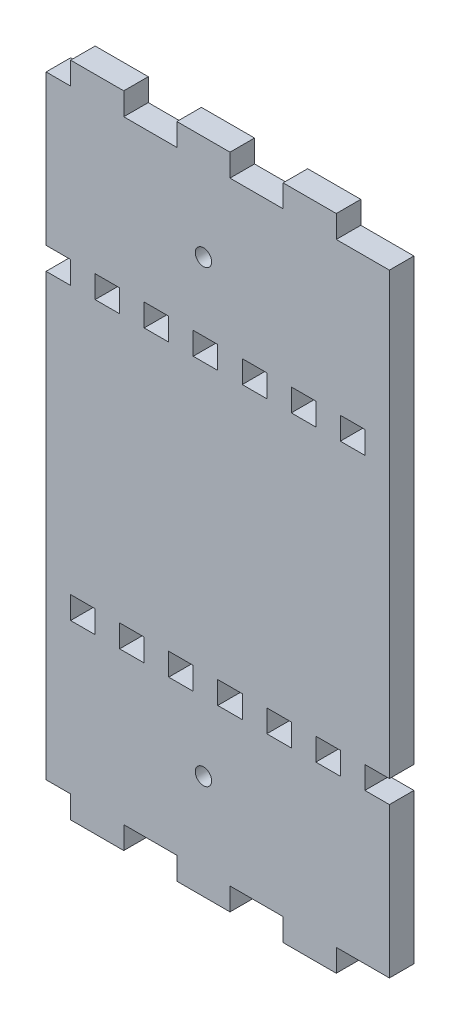
SolidWorks part; units mm, degrees
ref_plane "Front Plane" through (0, 0, 0) normal (0, 0, 1) x (1, 0, 0)
ref_plane "Top Plane" through (0, 0, 0) normal (0, 1, 0) x (1, 0, 0)
ref_plane "Right Plane" through (0, 0, 0) normal (1, 0, 0) x (0, 0, -1)
sketch "Model" plane through (0, 0, 0) normal (0, 0, 1) x (1, 0, 0)
  line L0 (-665.3097, 302.8745) -> (-665.3097, 339.6245)
  line L1 (-665.3097, 345.1245) -> (-665.3097, 452.8745)
  line L2 (-665.3097, 452.8745) -> (-678.3097, 452.8745)
  line L3 (-691.3097, 452.8745) -> (-704.3083, 452.8745)
  line L4 (-717.3083, 452.8745) -> (-730.3069, 452.8745)
  line L5 (-749.3097, 452.8745) -> (-749.3097, 416.1245)
  line L6 (-749.3097, 410.6245) -> (-749.3097, 302.8745)
  line L7 (-701.3097, 410.6245) -> (-695.3097, 410.6245)
  line L8 (-689.3097, 410.6245) -> (-683.3097, 410.6245)
  line L9 (-677.3097, 410.6245) -> (-671.3097, 410.6245)
  line L10 (-707.3097, 410.6245) -> (-713.3097, 410.6245)
  line L11 (-719.3097, 410.6245) -> (-725.3097, 410.6245)
  line L12 (-731.3097, 410.6245) -> (-737.3097, 410.6245)
  line L13 (-743.3097, 410.6245) -> (-749.3097, 410.6245)
  line L14 (-707.3097, 345.1245) -> (-701.3097, 345.1245)
  line L15 (-695.3097, 345.1245) -> (-689.3097, 345.1245)
  line L16 (-683.3097, 345.1245) -> (-677.3097, 345.1245)
  line L17 (-671.3097, 345.1245) -> (-665.3097, 345.1245)
  line L18 (-713.3097, 345.1245) -> (-719.3097, 345.1245)
  line L19 (-725.3097, 345.1245) -> (-731.3097, 345.1245)
  line L20 (-737.3097, 345.1245) -> (-743.3097, 345.1245)
  line L21 (-749.3097, 416.1245) -> (-743.3097, 416.1245)
  line L22 (-737.3097, 416.1245) -> (-731.3097, 416.1245)
  line L23 (-725.3097, 416.1245) -> (-719.3097, 416.1245)
  line L24 (-713.3097, 416.1245) -> (-707.3097, 416.1245)
  line L25 (-701.3097, 416.1245) -> (-695.3097, 416.1245)
  line L26 (-689.3097, 416.1245) -> (-683.3097, 416.1245)
  line L27 (-677.3097, 416.1245) -> (-671.3097, 416.1245)
  line L28 (-743.3097, 339.6245) -> (-737.3097, 339.6245)
  line L29 (-731.3097, 339.6245) -> (-725.3097, 339.6245)
  line L30 (-719.3097, 339.6245) -> (-713.3097, 339.6245)
  line L31 (-707.3097, 339.6245) -> (-701.3097, 339.6245)
  line L32 (-695.3097, 339.6245) -> (-689.3097, 339.6245)
  line L33 (-683.3097, 339.6245) -> (-677.3097, 339.6245)
  line L34 (-671.3097, 339.6245) -> (-665.3097, 339.6245)
  line L35 (-701.3097, 416.1245) -> (-701.3097, 410.6245)
  line L36 (-695.3097, 416.1245) -> (-695.3097, 410.6245)
  line L37 (-689.3097, 416.1245) -> (-689.3097, 410.6245)
  line L38 (-683.3097, 416.1245) -> (-683.3097, 410.6245)
  line L39 (-677.3097, 416.1245) -> (-677.3097, 410.6245)
  line L40 (-671.3097, 416.1245) -> (-671.3097, 410.6245)
  line L41 (-713.3097, 416.1245) -> (-713.3097, 410.6245)
  line L42 (-719.3097, 416.1245) -> (-719.3097, 410.6245)
  line L43 (-725.3097, 416.1245) -> (-725.3097, 410.6245)
  line L44 (-731.3097, 416.1245) -> (-731.3097, 410.6245)
  line L45 (-737.3097, 416.1245) -> (-737.3097, 410.6245)
  line L46 (-743.3097, 416.1245) -> (-743.3097, 410.6245)
  line L47 (-707.3097, 339.6245) -> (-707.3097, 345.1245)
  line L48 (-695.3097, 339.6245) -> (-695.3097, 345.1245)
  line L49 (-689.3097, 339.6245) -> (-689.3097, 345.1245)
  line L50 (-683.3097, 339.6245) -> (-683.3097, 345.1245)
  line L51 (-677.3097, 339.6245) -> (-677.3097, 345.1245)
  line L52 (-671.3097, 339.6245) -> (-671.3097, 345.1245)
  line L53 (-713.3097, 339.6245) -> (-713.3097, 345.1245)
  line L54 (-719.3097, 339.6245) -> (-719.3097, 345.1245)
  line L55 (-725.3097, 339.6245) -> (-725.3097, 345.1245)
  line L56 (-731.3097, 339.6245) -> (-731.3097, 345.1245)
  line L57 (-737.3097, 339.6245) -> (-737.3097, 345.1245)
  line L58 (-743.3097, 339.6245) -> (-743.3097, 345.1245)
  line L59 (-678.3097, 302.8758) -> (-678.3097, 297.3758)
  line L60 (-678.3097, 302.8758) -> (-665.3097, 302.8745)
  line L61 (-691.3083, 297.3771) -> (-678.3097, 297.3758)
  line L62 (-691.3097, 302.8758) -> (-691.3083, 297.3771)
  line L63 (-704.3083, 302.8771) -> (-704.3083, 297.3771)
  line L64 (-704.3083, 302.8771) -> (-691.3097, 302.8758)
  line L65 (-717.3069, 297.3784) -> (-704.3083, 297.3771)
  line L66 (-717.3083, 302.8771) -> (-717.3069, 297.3784)
  line L67 (-730.3069, 302.8784) -> (-730.3069, 297.3784)
  line L68 (-730.3069, 302.8784) -> (-717.3083, 302.8771)
  line L69 (-743.3056, 297.3797) -> (-730.3069, 297.3784)
  line L70 (-743.3056, 297.3797) -> (-743.305, 302.8745)
  line L71 (-743.305, 302.8745) -> (-749.3097, 302.8745)
  line L72 (-678.3097, 452.8745) -> (-678.3097, 458.3738)
  line L73 (-691.3083, 458.3725) -> (-678.3097, 458.3738)
  line L74 (-691.3097, 452.8745) -> (-691.3083, 458.3725)
  line L75 (-704.3083, 452.8745) -> (-704.3083, 458.3725)
  line L76 (-717.3069, 458.3712) -> (-704.3083, 458.3725)
  line L77 (-717.3083, 452.8745) -> (-717.3069, 458.3712)
  line L78 (-743.3056, 458.3699) -> (-730.3069, 458.3712)
  line L79 (-743.3056, 458.3699) -> (-743.305, 452.8751)
  line L80 (-749.3097, 452.8745) -> (-743.305, 452.8751)
  line L81 (-701.3097, 345.1245) -> (-701.3097, 339.6245)
  line L82 (-707.3097, 410.6245) -> (-707.3097, 416.1245)
  line L83 (-730.3069, 458.3712) -> (-730.3069, 452.8745)
  circle A0 centre (-710.8045, 322.8765) radius 2
  circle A1 centre (-710.8045, 432.873) radius 2
extrude "Boss-Extrude1" add sketch "Model" along normal blind 6 contours L10 L82 L24 L41 | L36 L25 L35 L7 | L38 L26 L37 L8 | L40 L27 L39 L9 | L58 L28 L57 L20 | L56 L29 L55 L19 | L54 L30 L53 L18 | L81 L14 L47 L31 | L32 L49 L15 L48 | L33 L51 L16 L50 | L5 L21 L46 L13 L6 L71 L70 L69 L67 L68 L66 L65 L63 L64 L62 L61 L59 L60 L0 L34 L52 L17 L1 L2 L72 L73 L74 L3 L75 L76 L77 L4 L83 L78 L79 L80 | L44 L12 L45 L22 | L43 L11 L42 L23 | A1 | A0
